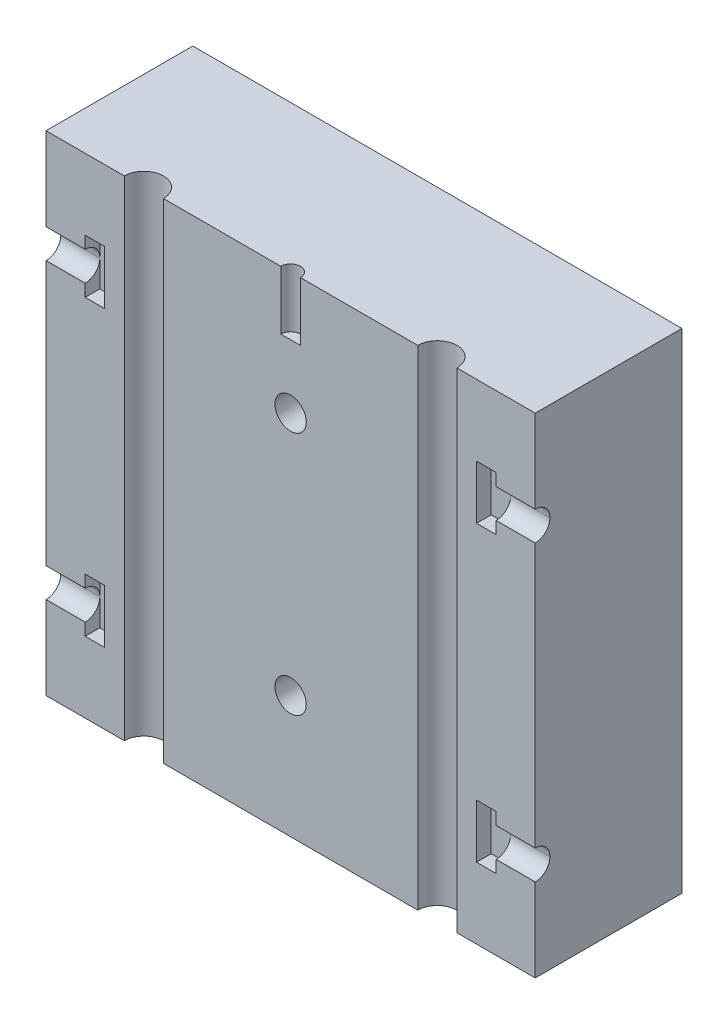
SolidWorks part; units mm, degrees
ref_plane "Plan de face" through (0, 0, 0) normal (0, 0, 1) x (1, 0, 0)
ref_plane "Plan de dessus" through (0, 0, 0) normal (0, 1, 0) x (1, 0, 0)
ref_plane "Plan de droite" through (0, 0, 0) normal (1, 0, 0) x (0, 0, -1)
sketch "Esquisse1" plane through (0, 0, 0) normal (0, 0, 1) x (1, 0, 0)
  line L0 (17.9177, 25) -> (30.2033, 25) construction
  line L1 (0, 0) -> (50, 0)
  line L2 (0, 0) -> (0, 50)
  line L3 (0, 50) -> (50, 50)
  line L4 (50, 0) -> (50, 50)
  line L5 (25, 82.493) -> (25, -3.859) construction
  line L6 (17.9177, 37.5) -> (30.2033, 37.5) construction
  circle A0 centre (25, 37.5) radius 1.6
  circle A1 centre (25, 12.5) radius 1.6
extrude "Extrusion1" add sketch "Esquisse1" along normal blind 15
sketch "Esquisse2" plane through (0, 50, 0) normal (0, 1, 0) x (-1, 0, 0)
  line L0 (-25, -2.8423) -> (-25, 10.3145) construction
  line L1 (-10, 10.3145) -> (-10, -1.749) construction
  line L2 (1.6579, 15) -> (-41.5071, 15) construction
  circle A0 centre (-10, 15) radius 2
  circle A1 centre (-40, 15) radius 2
  dimension "D1" = 15
extrude "Enlèv. mat.-Extru.1" cut sketch "Esquisse2" against normal through all
sketch "Esquisse3" plane through (0, 0, 15) normal (0, 0, 1) x (1, 0, 0)
  line L0 (-6.9611, 50) -> (52.882, 50) construction
  line L1 (-6.9611, 0) -> (52.882, 0) construction
  line L2 (0, 53.8943) -> (0, -3.9793) construction
  line L3 (25, 53.8943) -> (25, -3.0703) construction
  line L4 (-6.9611, 25) -> (55.003, 25) construction
  line L5 (-6.9611, 10) -> (34.3988, 10) construction
  line L6 (6, -3.0703) -> (6, 16.4853) construction
  line L7 (4, -3.0703) -> (4, 16.4853) construction
  line L8 (-6.6638, 11.5) -> (10.0386, 11.5) construction
  line L9 (-6.9611, 8.5) -> (10.0386, 8.5) construction
  line L10 (3.2114, 12.75) -> (6.4884, 12.75) construction
  line L11 (-1.135, 11.5) -> (4, 11.5)
  line L12 (-1.135, 11.5) -> (-1.135, 8.5)
  line L13 (-1.135, 8.5) -> (4, 8.5)
  line L14 (-1.135, 38.5) -> (-1.135, 41.5)
  line L15 (3.2114, 7.25) -> (6.4884, 7.25) construction
  line L16 (4, 8.5) -> (4, 7.25)
  line L17 (4, 12.75) -> (6, 12.75)
  line L18 (4, 12.75) -> (4, 11.5)
  line L19 (4, 7.25) -> (6, 7.25)
  line L20 (6, 12.75) -> (6, 7.25)
  line L21 (-1.135, 41.5) -> (4, 41.5)
  line L22 (-1.135, 38.5) -> (4, 38.5)
  line L23 (4, 37.25) -> (6, 37.25)
  line L24 (4, 37.25) -> (4, 38.5)
  line L25 (6, 37.25) -> (6, 42.75)
  line L26 (4, 42.75) -> (6, 42.75)
  line L27 (4, 41.5) -> (4, 42.75)
  line L28 (46, 42.75) -> (44, 42.75)
  line L29 (46, 41.5) -> (46, 42.75)
  line L30 (51.135, 41.5) -> (46, 41.5)
  line L31 (51.135, 38.5) -> (51.135, 41.5)
  line L32 (51.135, 38.5) -> (46, 38.5)
  line L33 (44, 37.25) -> (44, 42.75)
  line L34 (46, 37.25) -> (44, 37.25)
  line L35 (46, 37.25) -> (46, 38.5)
  line L36 (46, 12.75) -> (44, 12.75)
  line L37 (44, 12.75) -> (44, 7.25)
  line L38 (46, 7.25) -> (44, 7.25)
  line L39 (51.135, 8.5) -> (46, 8.5)
  line L40 (51.135, 11.5) -> (46, 11.5)
  line L41 (46, 12.75) -> (46, 11.5)
  line L42 (46, 8.5) -> (46, 7.25)
  line L43 (51.135, 11.5) -> (51.135, 8.5)
  dimension "D1" = 10
  dimension "D2" = 1.5
  dimension "D3" = 3
  dimension "D4" = 6
  dimension "D5" = 2
  dimension "D6" = 2.75
  dimension "D7" = 2.75
extrude "Enlèv. mat.-Extru.3" cut sketch "Esquisse3" against normal blind 1.5
fillet "Congé1" radius 1.49 1 edges at (2, 11.5, 13.5)
fillet "Congé2" radius 1.49 7 edges at (48, 11.5, 13.5) (48, 8.5, 13.5) (2, 8.5, 13.5) (2, 38.5, 13.5) (2, 41.5, 13.5) (48, 41.5, 13.5) (48, 38.5, 13.5)
sketch "Esquisse4" plane through (0, 50, 0) normal (0, 1, 0) x (-1, 0, 0)
  line L0 (-55.136, 15) -> (3.6621, 15) construction
  line L1 (-25, 22.9753) -> (-25, -4.8724) construction
  line L2 (0, -10.6125) -> (0, 22.9753) construction
  circle A0 centre (-25, 15) radius 1
  dimension "D1" = 25
extrude "Enlèv. mat.-Extru.4" cut sketch "Esquisse4" against normal blind 6
